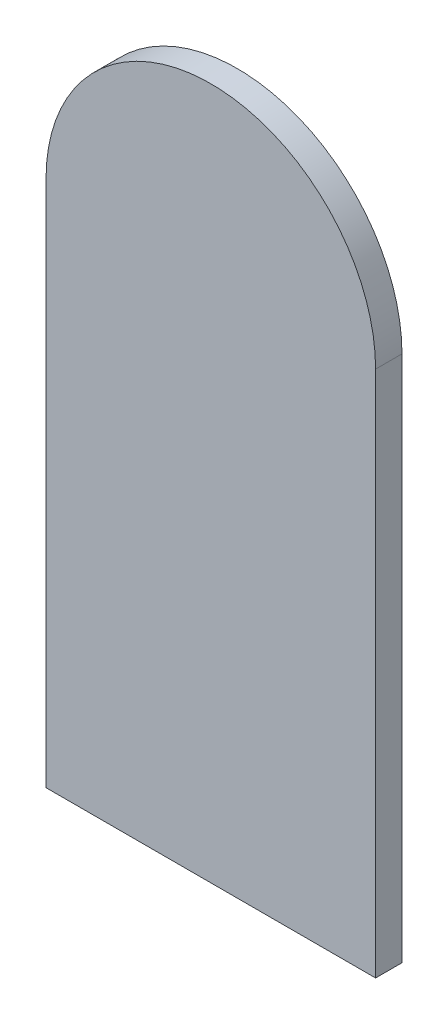
SolidWorks part; units mm, degrees
ref_plane "Front Plane" through (0, 0, 0) normal (0, 0, 1) x (1, 0, 0)
ref_plane "Top Plane" through (0, 0, 0) normal (0, 1, 0) x (1, 0, 0)
ref_plane "Right Plane" through (0, 0, 0) normal (1, 0, 0) x (0, 0, -1)
sketch "Sketch1" plane through (0, 0, 0) normal (0, 0, 1) x (1, 0, 0)
  line L0 (0, 0) -> (-12.5, 0)
  line L1 (-12.5, 0) -> (-12.5, 20)
  line L2 (0, 0) -> (0, 20)
  arc A0 (-12.5, 20) -> (0, 20) centre (-6.25, 20) cw
extrude "Boss-Extrude1" add sketch "Sketch1" along normal blind 1
